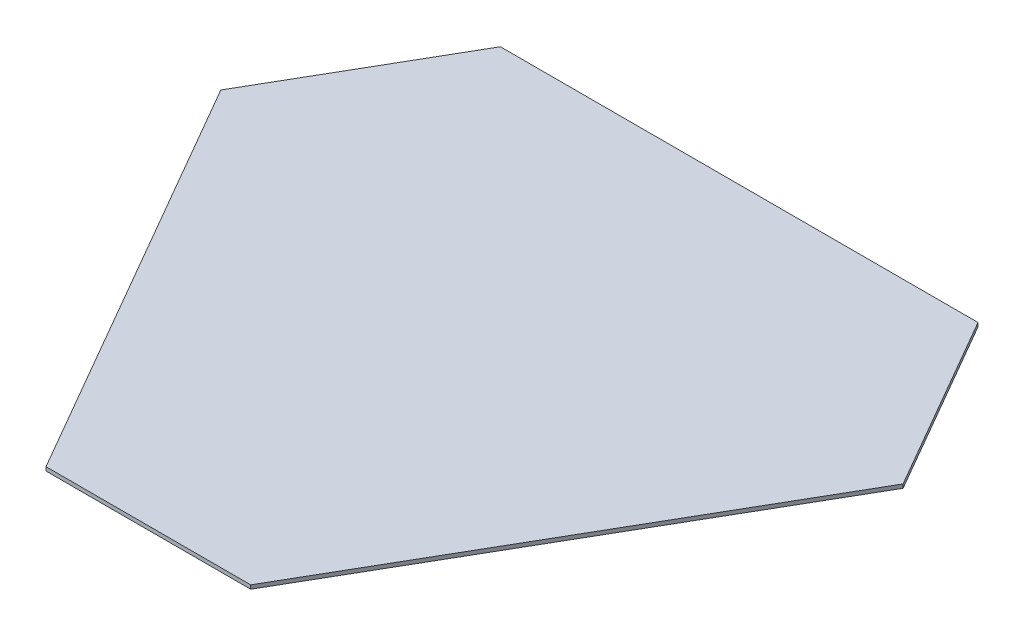
SolidWorks part; units mm, degrees
ref_plane "Front Plane" through (0, 0, 0) normal (0, 0, 1) x (1, 0, 0)
ref_plane "Top Plane" through (0, 0, 0) normal (0, 1, 0) x (1, 0, 0)
ref_plane "Right Plane" through (0, 0, 0) normal (1, 0, 0) x (0, 0, -1)
sketch "Sketch1" plane through (0, 0, 0) normal (0, 1, 0) x (1, 0, 0)
  line L0 (-106.25, 61.3435) -> (81.25, -46.9097) construction
  line L1 (87.5, 93.8194) -> (-87.5, 93.8194)
  line L2 (-87.5, 93.8194) -> (-125, 28.8675)
  line L3 (-125, 28.8675) -> (-37.5, -122.6869)
  line L4 (-37.5, -122.6869) -> (37.5, -122.6869)
  line L5 (37.5, -122.6869) -> (125, 28.8675)
  line L6 (125, 28.8675) -> (87.5, 93.8194)
  line L7 (106.25, 61.3435) -> (-81.25, -46.9097) construction
  line L8 (0, 93.8194) -> (0, -122.6869) construction
  line L9 (87.5, 93.8194) -> (-37.5, -122.6869) construction
  line L10 (-87.5, 93.8194) -> (37.5, -122.6869) construction
  line L11 (125, 28.8675) -> (-125, 28.8675) construction
  point P1 (0, 93.8194)
  point P8 (0, 0)
  point P14 (0, 0)
  point P16 (84.2334, 91.9335)
  dimension "D1" = 75
  dimension "D2" = 120
  dimension "D3" = 175
extrude "Boss-Extrude1" add sketch "Sketch1" along normal blind 1.4 contours L1 L2 L3 L4 L5 L6
